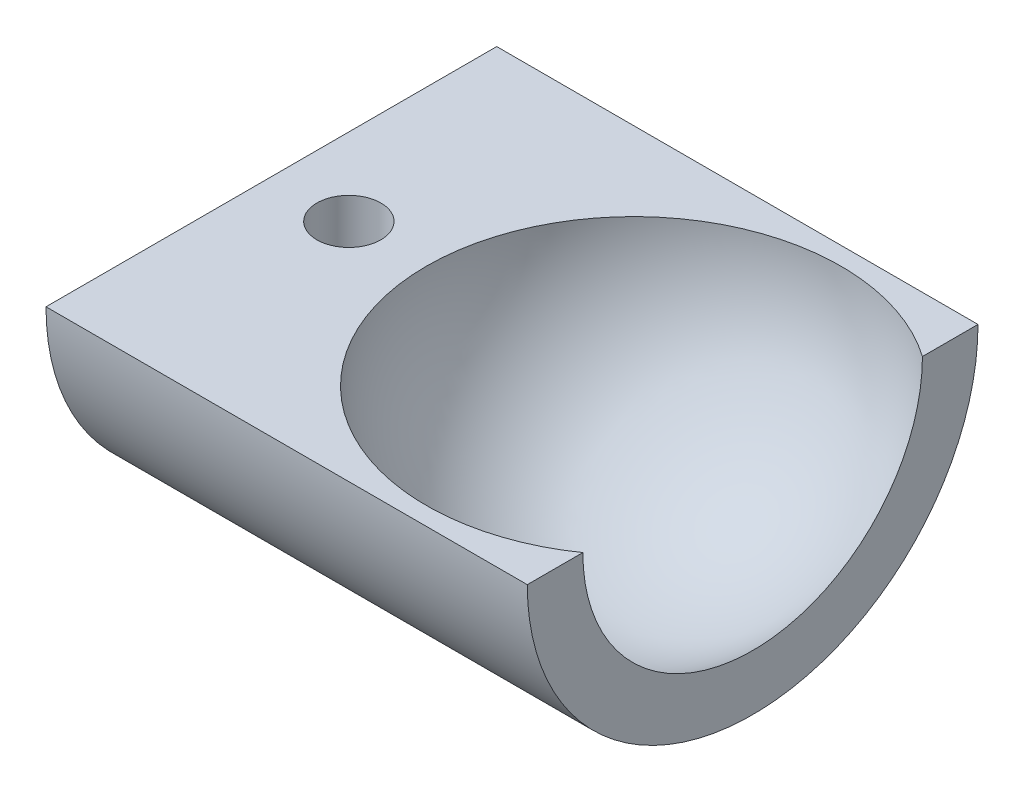
SolidWorks part; units mm, degrees
ref_plane "Alzado" through (0, 0, 0) normal (0, 0, 1) x (1, 0, 0)
ref_plane "Planta" through (0, 0, 0) normal (0, 1, 0) x (1, 0, 0)
ref_plane "Vista lateral" through (0, 0, 0) normal (1, 0, 0) x (0, 0, -1)
sketch "Croquis1" plane through (0, 0, 0) normal (0, 1, 0) x (1, 0, 0)
  line L0 (-10.7, 0) -> (-18.7, 0)
  line L1 (6.1397, 11.6308) -> (-18.7, 11.6308)
  line L3 (6.1397, 11.6308) -> (6.1397, 8.7632)
  line L4 (-18.7, 11.6308) -> (-18.7, 0)
  arc A1 (6.1397, 8.7632) -> (-10.7, 0) centre (0, 0) ccw
  dimension "D2" = 8
revolve "Revolución4" add sketch "Croquis1" angle 360 about L0
sketch "Croquis7" plane through (6.1397, 0, 0) normal (1, 0, 0) x (0, 0, -1)
  line L1 (0, 0) -> (14.104, 0)
  line L2 (14.104, 0) -> (14.104, 12.4724)
  line L3 (14.104, 12.4724) -> (-13.1941, 12.4724)
  line L4 (-13.1941, 12.4724) -> (-13.1941, 0)
  line L5 (-13.1941, 0) -> (0, 0)
extrude "Cortar-Extruir5" cut sketch "Croquis7" against normal blind 50
sketch "Croquis8" plane through (0, 0, 0) normal (0, 1, 0) x (1, 0, 0)
  line L1 (-10.7, 0) -> (-18.7, 0) construction
  circle A0 centre (-14.7, 0) radius 1.65
extrude "Cortar-Extruir6" cut sketch "Croquis8" against normal blind 50
